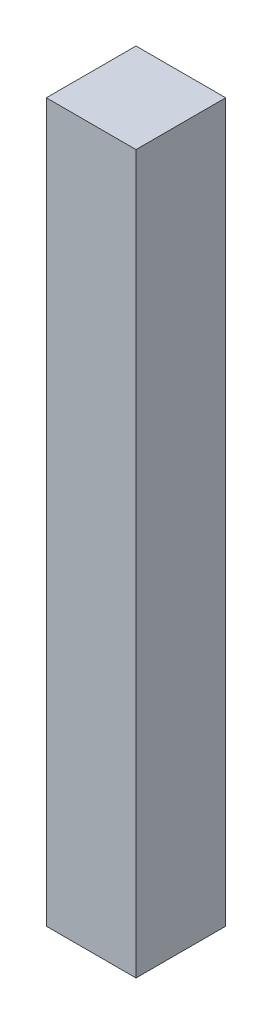
SolidWorks part; units mm, degrees
ref_plane "Front Plane" through (0, 0, 0) normal (0, 0, 1) x (1, 0, 0)
ref_plane "Top Plane" through (0, 0, 0) normal (0, 1, 0) x (1, 0, 0)
ref_plane "Right Plane" through (0, 0, 0) normal (1, 0, 0) x (0, 0, -1)
sketch "Sketch2" plane through (0, 0, 0) normal (0, 0, 1) x (1, 0, 0)
  line L0 (0, 0) -> (0, -160)
  line L1 (0, -160) -> (-20, -160)
  line L2 (-20, -160) -> (-20, 0)
  line L3 (-20, 0) -> (0, 0)
  dimension "D1" = 160
  dimension "D2" = 20
extrude "Boss-Extrude1" add sketch "Sketch2" along normal blind 20
